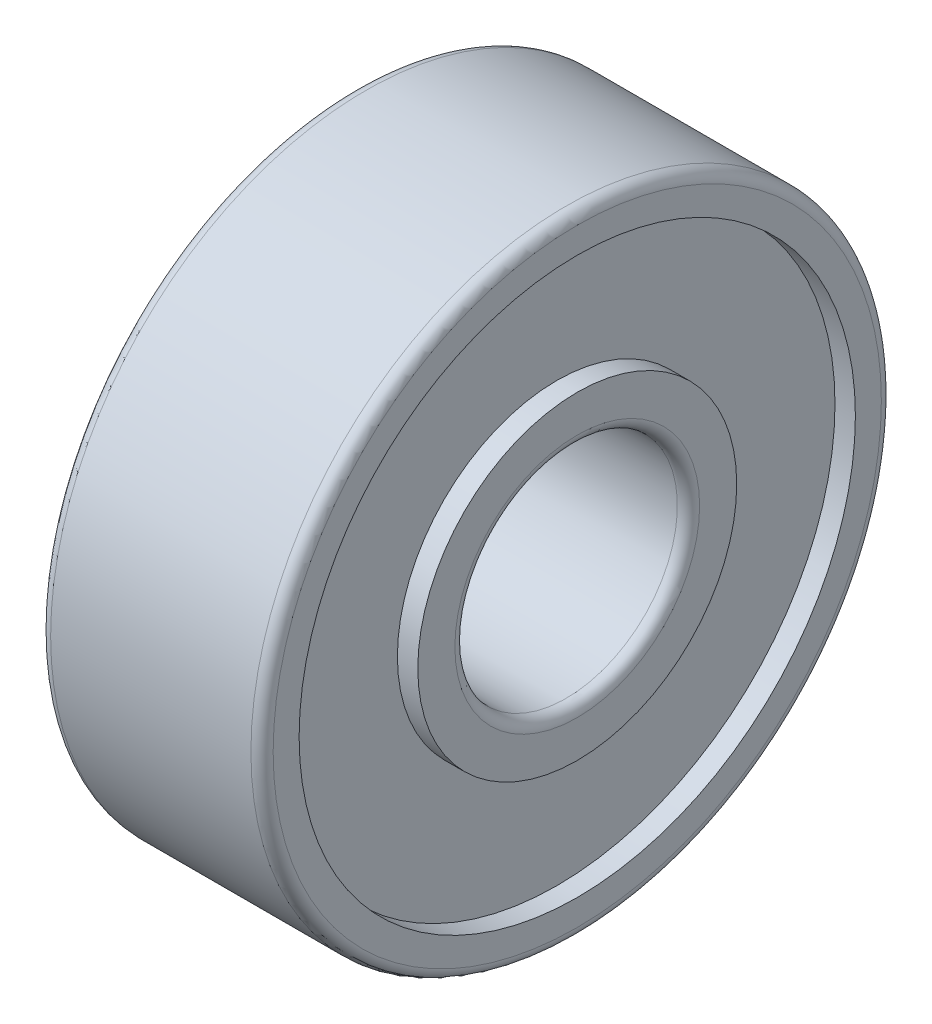
SolidWorks part; units mm, degrees
ref_plane "Front Plane" through (0, 0, 0) normal (0, 0, 1) x (1, 0, 0)
ref_plane "Top Plane" through (0, 0, 0) normal (0, 1, 0) x (1, 0, 0)
ref_plane "Right Plane" through (0, 0, 0) normal (1, 0, 0) x (0, 0, -1)
sketch "Sketch1" plane through (0, 0, 0) normal (0, 0, 1) x (1, 0, 0)
  line L0 (0, 0) -> (6, 0) construction
  line L1 (0, 3) -> (6, 3)
  line L2 (6, 3) -> (6, 4.3)
  line L3 (6, 4.3) -> (5.45, 4.3)
  line L4 (5.45, 4.3) -> (5.45, 7.5)
  line L5 (5.45, 7.5) -> (6, 7.5)
  line L6 (6, 7.5) -> (6, 8.5)
  line L7 (6, 8.5) -> (0, 8.5)
  line L8 (0, 8.5) -> (0, 7.5)
  line L9 (0, 7.5) -> (0.55, 7.5)
  line L10 (0.55, 7.5) -> (0.55, 4.3)
  line L11 (0.55, 4.3) -> (0, 4.3)
  line L12 (0, 4.3) -> (0, 3)
  dimension "D_s" = 6
  dimension "D" = 17
  dimension "B" = 6
  dimension "MSM_3" = 8.6
  dimension "MSM_4" = 15
  dimension "MSM_5" = 4.9
revolve "Revolve1" add sketch "Sketch1" angle 360 about L0
fillet "Fillet1" radius 0.3 4 edges at (0, 0, 3) (6, 0, 3) (0, 0, 8.5) (6, 0, 8.5)
